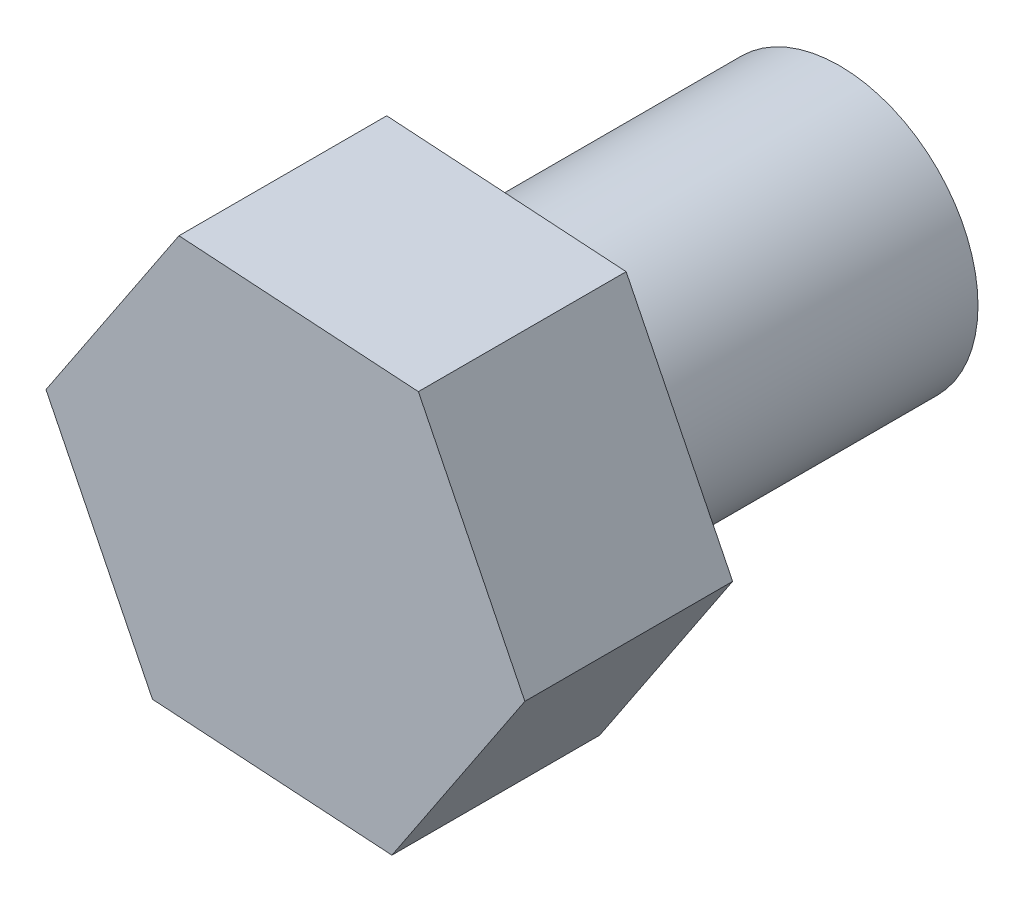
SolidWorks part; units mm, degrees
ref_plane "前视基准面" through (0, 0, 0) normal (0, 0, 1) x (1, 0, 0)
ref_plane "上视基准面" through (0, 0, 0) normal (0, 1, 0) x (1, 0, 0)
ref_plane "右视基准面" through (0, 0, 0) normal (1, 0, 0) x (0, 0, -1)
sketch "草图1" plane through (0, 0, 0) normal (0, 0, 1) x (1, 0, 0)
  line L1 (1.5374, -3.1043) -> (3.4571, -0.2207)
  line L2 (3.4571, -0.2207) -> (1.9197, 2.8835)
  line L3 (1.9197, 2.8835) -> (-1.5374, 3.1043)
  line L4 (-1.5374, 3.1043) -> (-3.4571, 0.2207)
  line L5 (-3.4571, 0.2207) -> (-1.9197, -2.8835)
  line L6 (-1.9197, -2.8835) -> (1.5374, -3.1043)
  circle A0 centre (0, 0) radius 3 construction
  dimension "D1" = 6
extrude "凸台-拉伸1" add sketch "草图1" along normal blind 3
sketch "草图2" plane through (0, 0, 0) normal (0, 0, -1) x (-1, 0, 0)
  circle A0 centre (0, 0) radius 2
extrude "凸台-拉伸2" add sketch "草图2" along normal blind 5
